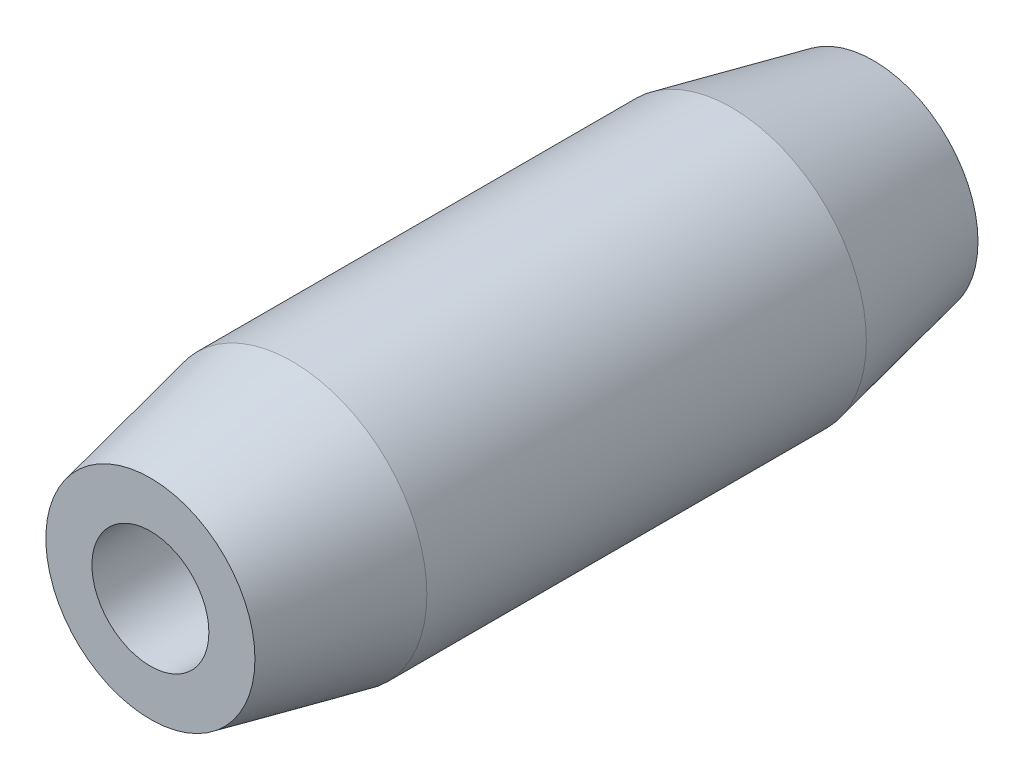
SolidWorks part; units mm, degrees
material "ABS"
ref_plane "Front Plane" through (0, 0, 0) normal (0, 0, 1) x (1, 0, 0)
ref_plane "Top Plane" through (0, 0, 0) normal (0, 1, 0) x (1, 0, 0)
ref_plane "Right Plane" through (0, 0, 0) normal (1, 0, 0) x (0, 0, -1)
sketch "Sketch1" plane through (0, 0, 0) normal (0, 0, 1) x (1, 0, 0)
  circle A0 centre (0, 0) radius 3.8
  circle A1 centre (0, 0) radius 1.65
  dimension "D1" = 3.3
  dimension "D2" = 7.6
extrude "Boss-Extrude1" add sketch "Sketch1" along normal blind 20.4
chamfer "Chamfer1" distance 4 angle 12 1 edges at (3.8, 0, 20.4)
chamfer "Chamfer2" distance 4 angle 12 1 edges at (3.8, 0, 0)
